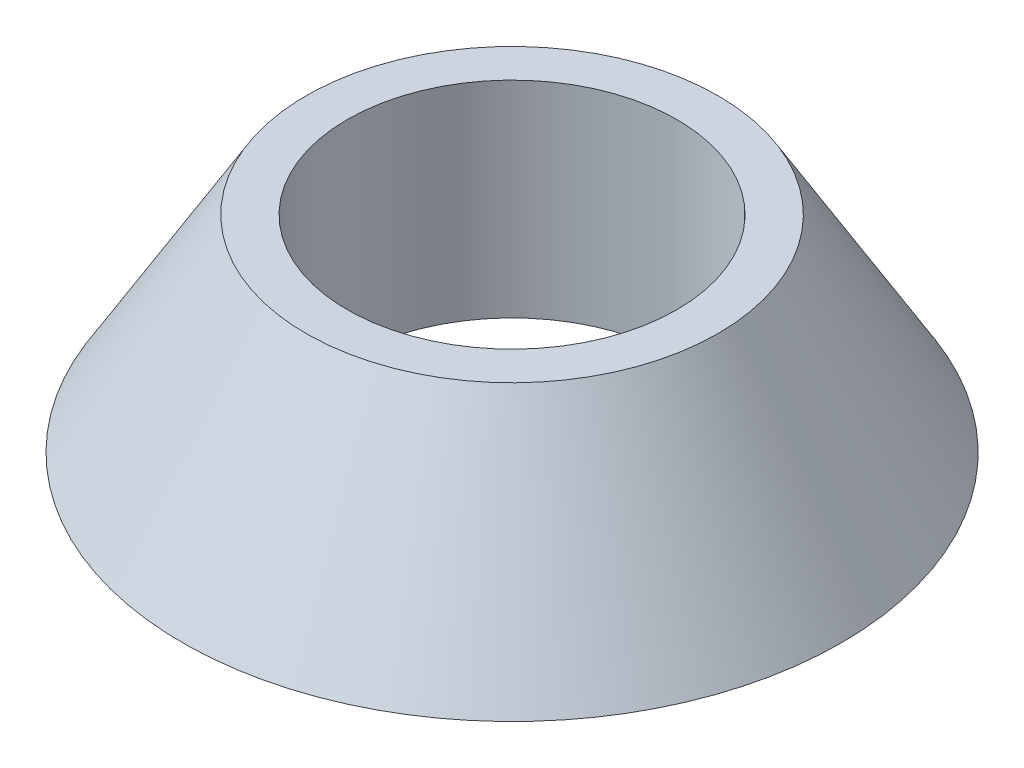
SolidWorks part; units mm, degrees
ref_plane "Płaszczyzna XY" through (0, 0, 0) normal (0, 0, 1) x (1, 0, 0)
ref_plane "Płaszczyzna XZ" through (0, 0, 0) normal (0, 1, 0) x (1, 0, 0)
ref_plane "Płaszczyzna YZ" through (0, 0, 0) normal (1, 0, 0) x (0, 0, -1)
sketch "Szkic1" plane through (0, 0, 0) normal (0, 0, 1) x (1, 0, 0)
  line L0 (0, 0) -> (0, 5.4167) construction
  line L1 (4, 0) -> (4, 5)
  line L3 (8, 0) -> (4, 0)
  line L4 (4, 5) -> (5, 5)
  line L5 (5, 5) -> (8, 0)
  dimension "D1" = 5
  dimension "D2" = 4
  dimension "D3" = 8
  dimension "D4" = 1
revolve "Obrót1" add sketch "Szkic1" angle 360 about L0
